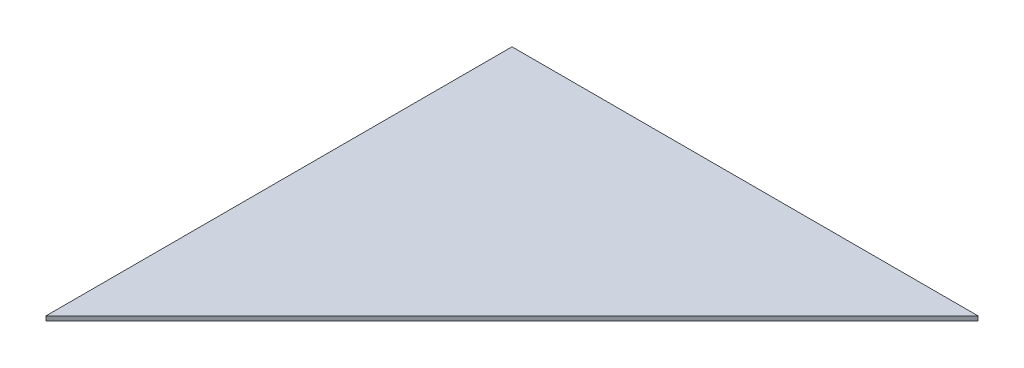
SolidWorks part; units mm, degrees
material "Oak"
ref_plane "Front Plane" through (0, 0, 0) normal (0, 0, 1) x (1, 0, 0)
ref_plane "Top Plane" through (0, 0, 0) normal (0, 1, 0) x (1, 0, 0)
ref_plane "Right Plane" through (0, 0, 0) normal (1, 0, 0) x (0, 0, -1)
sketch "Sketch1" plane through (0, 0, 0) normal (0, 1, 0) x (1, 0, 0)
  line L1 (-609.6, -609.6) -> (609.6, -609.6)
  line L2 (-609.6, -609.6) -> (-609.6, 609.6)
  line L3 (-609.6, 609.6) -> (609.6, 609.6)
  line L4 (609.6, -609.6) -> (609.6, 609.6)
  line L5 (-609.6, -609.6) -> (609.6, 609.6) construction
  line L6 (-609.6, 609.6) -> (609.6, -609.6) construction
  point P0 (0, 0)
  dimension "D1" = 1219.2
extrude "Boss-Extrude1" add sketch "Sketch1" along normal blind 5.5562
sketch "Sketch2" plane through (0, 0, 0) normal (0, -1, 0) x (1, 0, 0)
  line L1 (-52.8241, -609.6) -> (-609.6, -52.8241)
  line L4 (-609.6, -52.8241) -> (-609.6, -609.6)
  line L5 (-609.6, 609.6) -> (609.6, 609.6)
  line L6 (609.6, 609.6) -> (609.6, -609.6)
  line L7 (609.6, -609.6) -> (-52.8241, -609.6)
  line L8 (-609.6, -52.8241) -> (-609.6, 609.6)
  line L9 (-609.6, -609.6) -> (-52.8241, -609.6)
  line M1 (609.6, -609.6) -> (609.6, 609.6)
  line M2 (609.6, 609.6) -> (-609.6, 609.6)
  line M3 (-609.6, 609.6) -> (-609.6, -609.6)
  line M4 (-609.6, -609.6) -> (609.6, -609.6)
extrude "Cut-Extrude1" cut sketch "Sketch2" against normal through all contours L1 M4 M1 M2 M3
